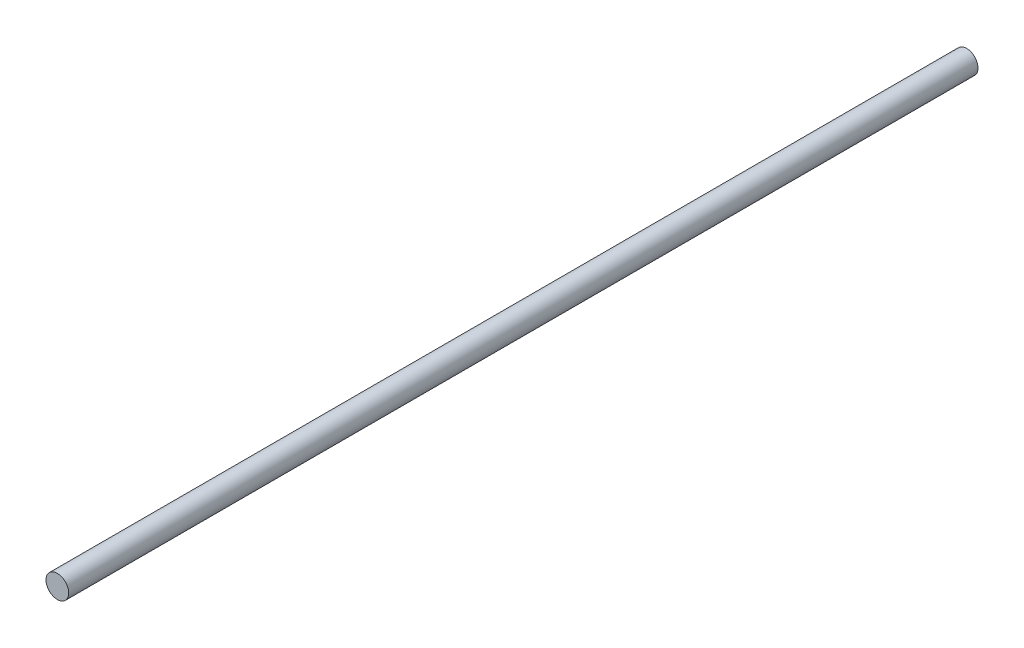
SolidWorks part; units mm, degrees
material "AISI 1020"
ref_plane "Front Plane" through (0, 0, 0) normal (0, 0, 1) x (1, 0, 0)
ref_plane "Top Plane" through (0, 0, 0) normal (0, 1, 0) x (1, 0, 0)
ref_plane "Right Plane" through (0, 0, 0) normal (1, 0, 0) x (0, 0, -1)
sketch "Sketch1" plane through (0, 0, 0) normal (0, 0, 1) x (1, 0, 0)
  circle A0 centre (-8.7611, 6.9241) radius 5
  dimension "D1" = 10
extrude "Boss-Extrude1" add sketch "Sketch1" along normal blind 400
